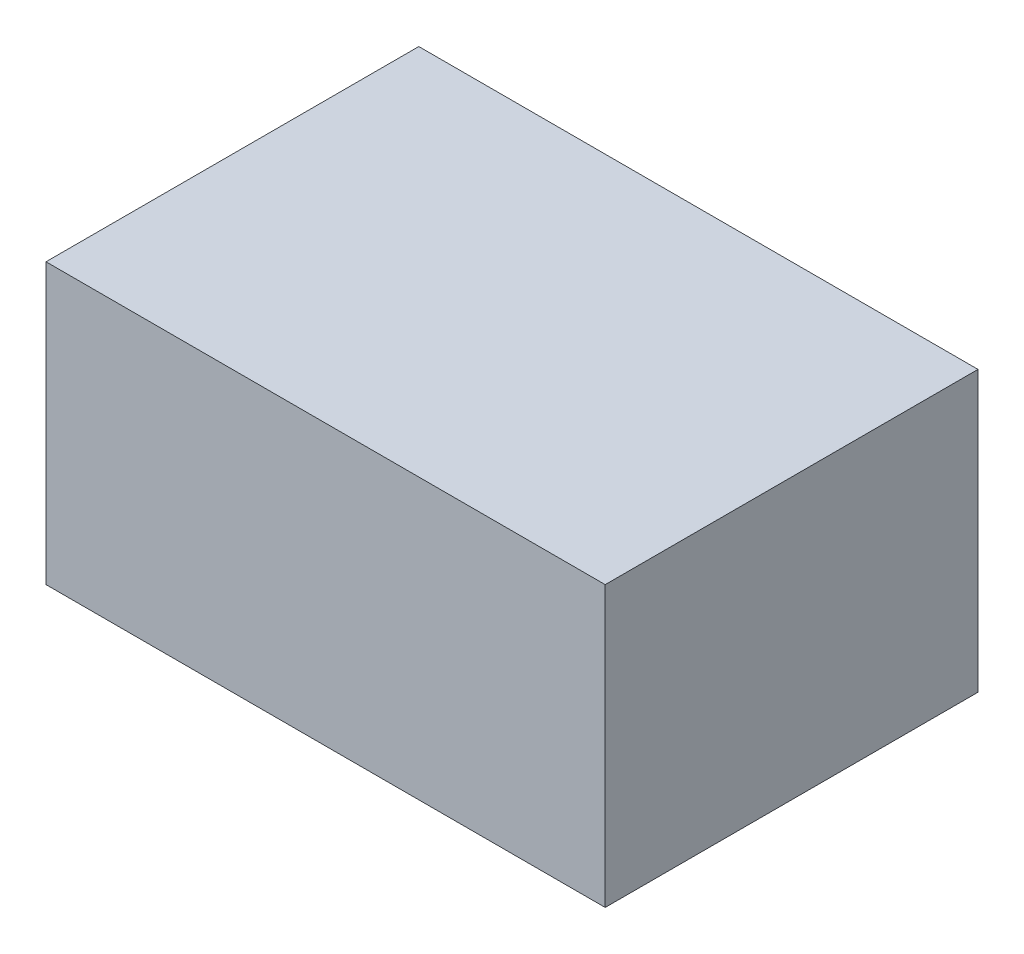
SolidWorks part; units mm, degrees
ref_plane "Front Plane" through (0, 0, 0) normal (0, 0, 1) x (1, 0, 0)
ref_plane "Top Plane" through (0, 0, 0) normal (0, 1, 0) x (1, 0, 0)
ref_plane "Right Plane" through (0, 0, 0) normal (1, 0, 0) x (0, 0, -1)
sketch "Sketch1" plane through (0, 0, 0) normal (0, 1, 0) x (1, 0, 0)
  line L1 (-40.3235, 28.9706) -> (19.6765, 28.9706)
  line L2 (-40.3235, 28.9706) -> (-40.3235, -11.0294)
  line L3 (-40.3235, -11.0294) -> (19.6765, -11.0294)
  line L4 (19.6765, 28.9706) -> (19.6765, -11.0294)
  dimension "D1" = 60
  dimension "D2" = 40
extrude "Boss-Extrude1" add sketch "Sketch1" along normal blind 30
